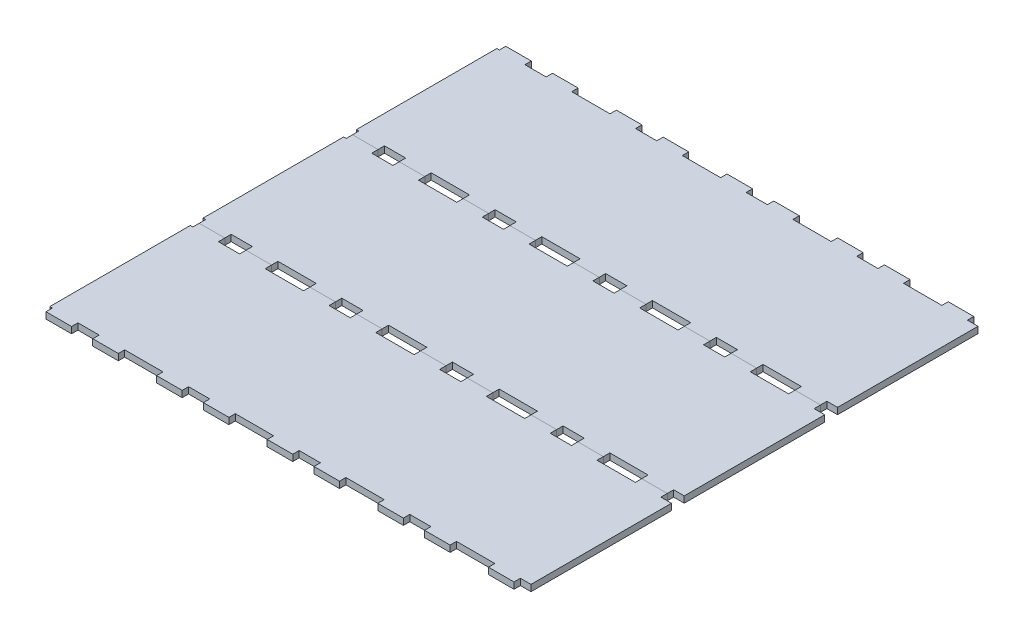
SolidWorks part; units mm, degrees
material "Cedar"
ref_plane "Front Plane" through (0, 0, 0) normal (0, 0, 1) x (1, 0, 0)
ref_plane "Top Plane" through (0, 0, 0) normal (0, 1, 0) x (1, 0, 0)
ref_plane "Right Plane" through (0, 0, 0) normal (1, 0, 0) x (0, 0, -1)
sketch "Sketch1" plane through (0, 0, 0) normal (0, 1, 0) x (1, 0, 0)
  line L1 (-258.4653, 76.2) -> (258.4653, 76.2)
  line L2 (-258.4653, 76.2) -> (-258.4653, -76.2)
  line L3 (-258.4653, -76.2) -> (258.4653, -76.2)
  line L4 (258.4653, 76.2) -> (258.4653, -76.2)
  line L5 (-258.4653, 76.2) -> (258.4653, -76.2) construction
  line L6 (-258.4653, -76.2) -> (258.4653, 76.2) construction
  point P0 (0, 0)
  dimension "D1" = 516.9306
  dimension "D2" = 152.4
extrude "Boss-Extrude1" add sketch "Sketch1" along normal blind 6.35
sketch "Sketch2" plane through (0, 6.35, 0) normal (0, 1, 0) x (1, 0, 0)
  line L0 (0, -76.2) -> (0, -69.85) construction
  line L1 (-23.2426, -69.85) -> (23.2426, -69.85) construction
  line L2 (-35.9426, -69.85) -> (-10.5426, -69.85) construction
  line L3 (-35.9426, -69.85) -> (-35.9426, -76.2) construction
  line L4 (-35.9426, -76.2) -> (-10.5426, -76.2) construction
  line L5 (-10.5426, -69.85) -> (-10.5426, -76.2)
  line L6 (-35.9426, -69.85) -> (-10.5426, -76.2) construction
  line L7 (-35.9426, -76.2) -> (-10.5426, -69.85) construction
  line L8 (-258.4653, -76.2) -> (258.4653, -76.2) construction
  line L9 (-10.5426, -69.85) -> (10.5426, -69.85)
  line L10 (10.5426, -69.85) -> (35.9426, -69.85) construction
  line L11 (10.5426, -69.85) -> (10.5426, -76.2)
  line L12 (10.5426, -76.2) -> (35.9426, -76.2) construction
  line L13 (35.9426, -69.85) -> (35.9426, -76.2) construction
  line L14 (10.5426, -69.85) -> (35.9426, -76.2) construction
  line L15 (10.5426, -76.2) -> (35.9426, -69.85) construction
  line L16 (10.5426, -76.2) -> (-10.5426, -76.2)
  line L17 (-35.9426, -76.2) -> (-35.9426, -69.85)
  line L18 (-35.9426, -69.85) -> (-54.9926, -69.85)
  line L19 (-54.9926, -69.85) -> (-54.9926, -76.2)
  line L20 (-54.9926, -76.2) -> (-35.9426, -76.2)
  line L21 (35.9426, -69.85) -> (54.9926, -69.85)
  line L22 (54.9926, -69.85) -> (54.9926, -76.2)
  line L23 (54.9926, -76.2) -> (35.9426, -76.2)
  line L24 (35.9426, -76.2) -> (35.9426, -69.85)
  point P5 (0, -69.85)
  point P6 (-23.2426, -73.025)
  point P11 (-23.2426, -69.85)
  point P17 (23.2426, -73.025)
  point P24 (23.2426, -69.85)
  dimension "D1" = 21.0852
  dimension "D2" = 25.4
  dimension "D3" = 6.35
  dimension "D4" = 54.9926
  dimension "D5" = 25.4
  dimension "D6" = 6.35
  dimension "D7" = 54.9926
extrude "Cut-Extrude1" cut sketch "Sketch2" against normal through all
pattern_linear "LPattern1" count 3 spacing 109.9852 along (1, 0, 0) count 3 spacing 109.9852 along (-1, 0, 0) of "Cut-Extrude1"
mirror "Mirror1" about plane through (0, 0, 0) normal (0, 0, 1) of "LPattern1", "Cut-Extrude1"
sketch "Sketch3" plane through (0, 6.35, 0) normal (0, 1, 0) x (1, 0, 0)
  line L0 (219.9705, 69.85) -> (219.9705, -76.2)
  line L1 (230.5131, 69.85) -> (209.4278, 69.85) construction
  line L2 (219.9705, -76.2) -> (258.4653, -76.2)
  line L3 (258.4653, -76.2) -> (258.4653, 76.2)
  line L4 (258.4653, 76.2) -> (219.9705, 76.2)
  line L5 (219.9705, 76.2) -> (219.9705, 69.85)
extrude "Cut-Extrude2" cut sketch "Sketch3" against normal through all
pattern_linear "LPattern2" count 3 spacing 152.4 along (0, 0, 1) of bodies 105
